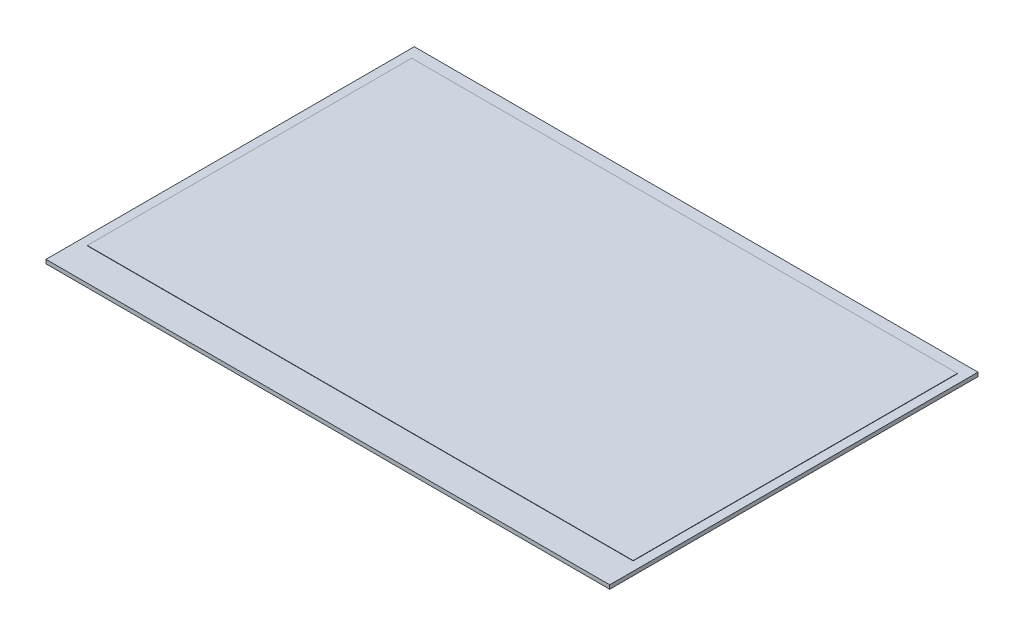
SolidWorks part; units mm, degrees
ref_plane "前基準面" through (0, 0, 0) normal (0, 0, 1) x (1, 0, 0)
ref_plane "上基準面" through (0, 0, 0) normal (0, 1, 0) x (1, 0, 0)
ref_plane "右基準面" through (0, 0, 0) normal (1, 0, 0) x (0, 0, -1)
sketch "草圖1" plane through (0, 0, 0) normal (0, 1, 0) x (1, 0, 0)
  line L1 (-85.1, 55.6) -> (85.1, 55.6)
  line L2 (-85.1, 55.6) -> (-85.1, -55.6)
  line L3 (-85.1, -55.6) -> (85.1, -55.6)
  line L4 (85.1, 55.6) -> (85.1, -55.6)
  line L5 (-85.1, 55.6) -> (85.1, -55.6) construction
  line L6 (-85.1, -55.6) -> (85.1, 55.6) construction
  point P0 (0, 0)
  dimension "D1" = 111.2
  dimension "D2" = 170.2
extrude "填料-伸長1" add sketch "草圖1" along normal blind 1.18
sketch "草圖2" plane through (0, 1.18, 0) normal (0, 1, 0) x (1, 0, 0)
  line L0 (85.1, 55.6) -> (-85.1, 55.6) construction
  line L1 (-82.4, 52.1) -> (82.4, 52.1)
  line L2 (-82.4, 52.1) -> (-82.4, -45.82)
  line L3 (-82.4, -45.82) -> (82.4, -45.82)
  line L4 (82.4, 52.1) -> (82.4, -45.82)
  line L5 (-82.4, 52.1) -> (82.4, -45.82) construction
  line L6 (-82.4, -45.82) -> (82.4, 52.1) construction
  line L7 (-78.9877, -45.569) -> (82.149, -45.569) construction
  point P0 (0, 3.14)
  dimension "D1" = 164.8
  dimension "D2" = 97.92
  dimension "D3" = 3.5
extrude "填料-伸長2" add sketch "草圖2" along normal blind 0.1
